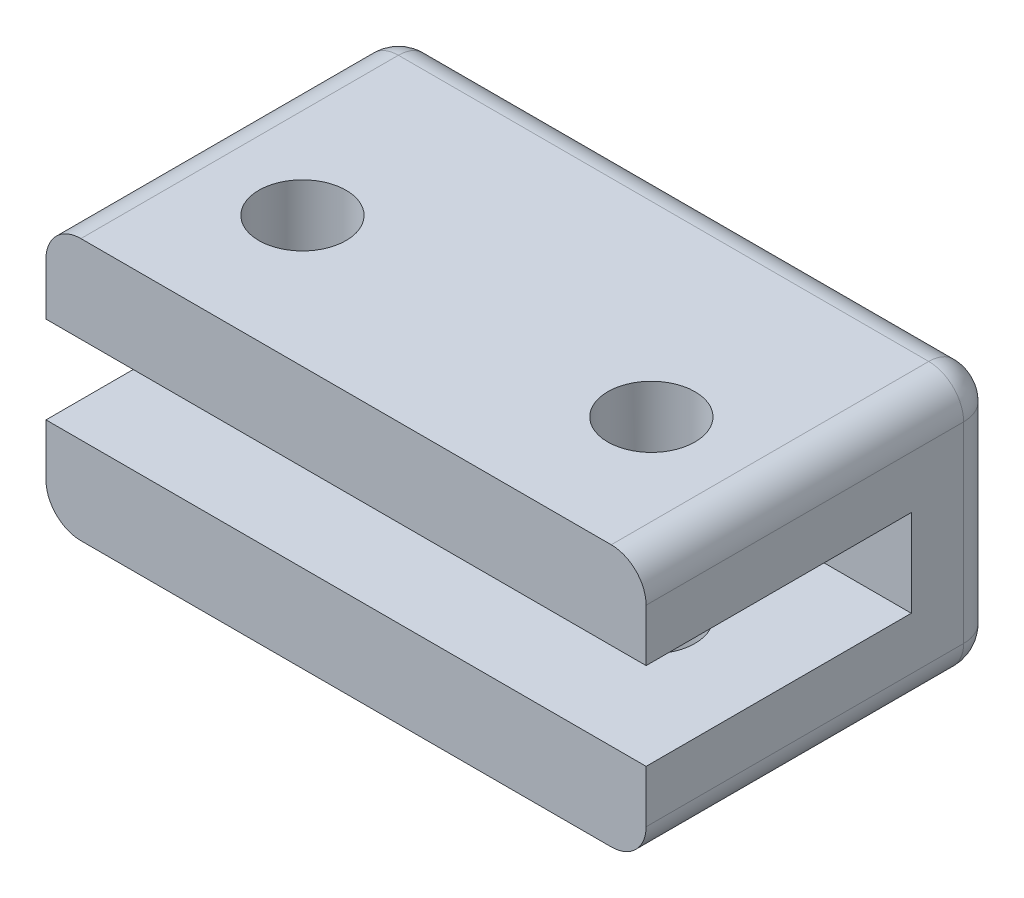
SolidWorks part; units mm, degrees
ref_plane "Front Plane" through (0, 0, 0) normal (0, 0, 1) x (1, 0, 0)
ref_plane "Top Plane" through (0, 0, 0) normal (0, 1, 0) x (1, 0, 0)
ref_plane "Right Plane" through (0, 0, 0) normal (1, 0, 0) x (0, 0, -1)
sketch "Sketch1" plane through (0, 0, 0) normal (0, 1, 0) x (1, 0, 0)
  line L1 (0, 12.7) -> (2.0955, 12.7)
  line L2 (0, 12.7) -> (0, 0)
  line L3 (0, 0) -> (2.0955, 0)
  line L4 (2.0955, 12.7) -> (2.0955, 0)
  dimension "D1" = 12.7
  dimension "D2" = 2.0955
revolve "Revolve1" add sketch "Sketch1" angle 360 about L2
sketch "Sketch2" plane through (0, 0, 0) normal (0, 0, 1) x (1, 0, 0)
  line L0 (0, 4.7625) -> (0, -4.7625) construction
  line L1 (-10.922, 4.7625) -> (10.922, 4.7625)
  line L2 (-10.922, 4.7625) -> (-10.922, -4.7625)
  line L3 (-10.922, -4.7625) -> (10.922, -4.7625)
  line L4 (10.922, 4.7625) -> (10.922, -4.7625)
  line L5 (-10.922, 0) -> (10.922, 0) construction
  dimension "D1" = 9.525
  dimension "D2" = 21.844
extrude "Boss-Extrude1" add sketch "Sketch2" along normal blind 12.827
fillet "Fillet4" radius 1.27 8 edges at (-10.922, -4.7625, 6.4135) (10.922, -4.7625, 6.4135) (0, -4.7625, 0) (-10.922, 4.7625, 6.4135) (10.922, 4.7625, 6.4135) (10.922, 0, 0) (-10.922, 0, 0) (0, 4.7625, 0)
sketch "Sketch3" plane through (-10.922, 0, 0) normal (-1, 0, 0) x (0, 0, 1)
  line L0 (12.827, 3.4925) -> (12.827, -3.4925) construction
  line L1 (3.175, 1.5875) -> (12.827, 1.5875)
  line L2 (3.175, 1.5875) -> (3.175, -1.5875)
  line L3 (3.175, -1.5875) -> (12.827, -1.5875)
  line L4 (12.827, 1.5875) -> (12.827, -1.5875)
  point P4 (12.827, 0)
  point P5 (12.827, 0)
  dimension "D1" = 3.175
  dimension "D2" = 9.652
extrude "Cut-Extrude1" cut sketch "Sketch3" against normal through all
sketch "Sketch4" plane through (0, 4.7625, 0) normal (0, 1, 0) x (1, 0, 0)
  line L0 (0, -1.27) -> (0, -12.827) construction
  line L1 (9.652, -1.27) -> (-9.652, -1.27) construction
  line L2 (9.652, -12.827) -> (-9.652, -12.827) construction
  circle A0 centre (-6.35, -8.0645) radius 1.5875
  circle A1 centre (6.35, -8.0645) radius 1.5875
  dimension "D2" = 3.175
  dimension "D1" = 4.7625
  dimension "D3" = 6.35
extrude "Cut-Extrude2" cut sketch "Sketch4" against normal through all
sketch "Sketch5" plane through (0, 0, 0) normal (0, 0, -1) x (-1, 0, 0)
  circle A0 centre (0, 0) radius 1.1303
  dimension "D1" = 2.2606
extrude "Cut-Extrude3" cut sketch "Sketch5" against normal up to next
sketch "Sketch6" plane through (0, 4.7625, 0) normal (0, 1, 0) x (1, 0, 0)
  line L0 (2.0955, 12.7) -> (-2.0955, 12.7) construction
  line L1 (-2.0955, 12.7) -> (-2.0955, 0) construction
  line L2 (2.0955, 0) -> (2.0955, 12.7) construction
  line L3 (2.0955, 12.7) -> (-2.0955, 12.7)
  line L4 (-2.0955, 12.7) -> (-2.0955, 0)
  line L5 (2.0955, 0) -> (2.0955, 12.7)
  line L6 (-2.0955, 0) -> (2.0955, 0)
extrude "Cut-Extrude4" cut sketch "Sketch6" against normal through all
